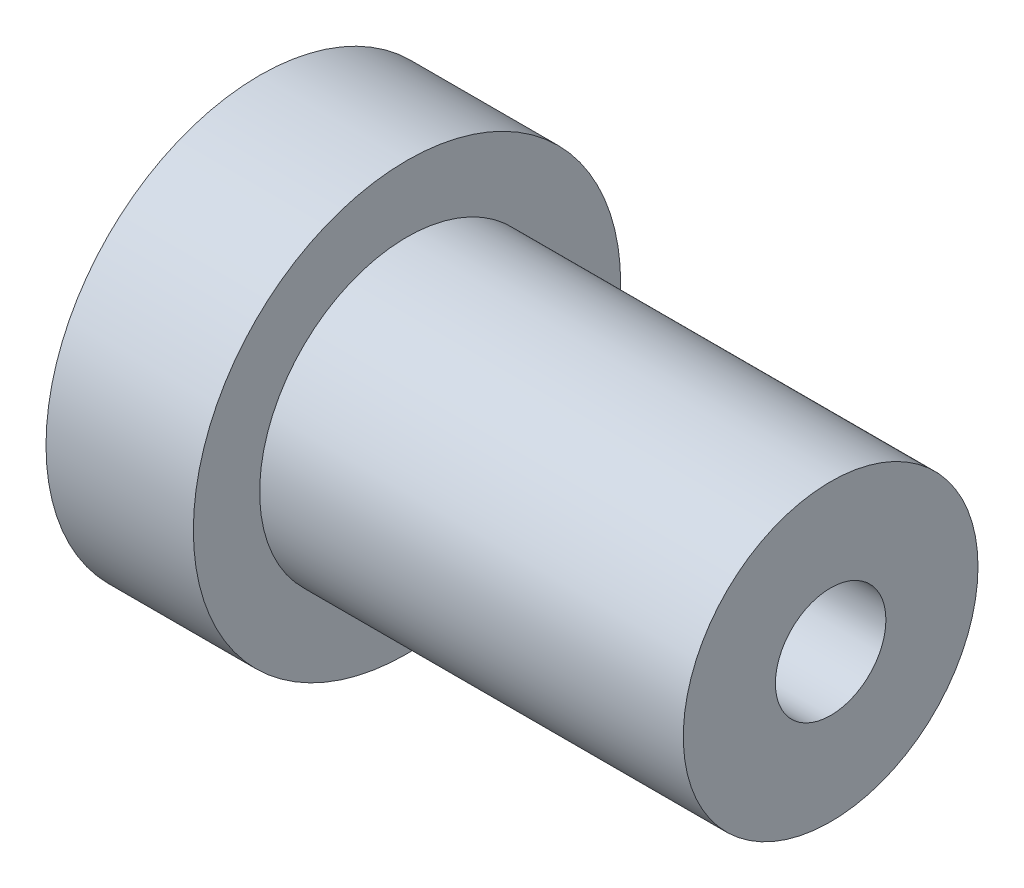
SolidWorks part; units mm, degrees
ref_plane "Front Plane" through (0, 0, 0) normal (0, 0, 1) x (1, 0, 0)
ref_plane "Top Plane" through (0, 0, 0) normal (0, 1, 0) x (1, 0, 0)
ref_plane "Right Plane" through (0, 0, 0) normal (1, 0, 0) x (0, 0, -1)
sketch "Sketch1" plane through (0, 0, 0) normal (1, 0, 0) x (0, 0, -1)
  circle A0 centre (0, 0) radius 5.8
extrude "Boss-Extrude1" add sketch "Sketch1" along normal blind 4
sketch "Sketch2" plane through (4, 0, 0) normal (1, 0, 0) x (0, 0, -1)
  circle A0 centre (0, 0) radius 4
extrude "Boss-Extrude2" add sketch "Sketch2" along normal blind 11.5
sketch "Sketch3" plane through (0, 0, 0) normal (-1, 0, 0) x (0, 0, 1)
  circle A0 centre (0, 0) radius 1.5
extrude "Cut-Extrude1" cut sketch "Sketch3" against normal blind 20
sketch "Sketch4" plane through (0, 0, 0) normal (-1, 0, 0) x (0, 0, 1)
  circle A0 centre (0, 0) radius 3
extrude "Cut-Extrude2" cut sketch "Sketch4" against normal blind 3
